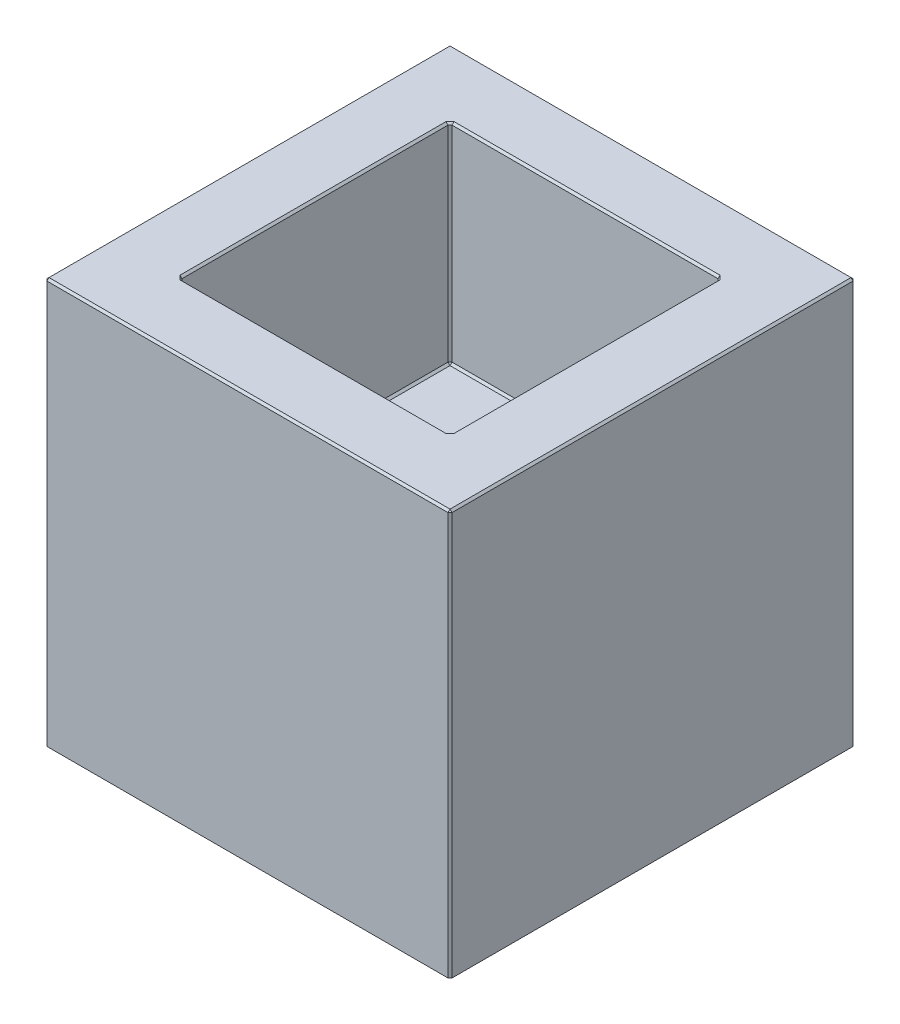
SolidWorks part; units mm, degrees
ref_plane "Plan de face" through (0, 0, 0) normal (0, 0, 1) x (1, 0, 0)
ref_plane "Plan de dessus" through (0, 0, 0) normal (0, 1, 0) x (1, 0, 0)
ref_plane "Plan de droite" through (0, 0, 0) normal (1, 0, 0) x (0, 0, -1)
sketch "Esquisse2" plane through (0, 0, 0) normal (0, 1, 0) x (1, 0, 0)
  line L1 (-3, -3) -> (3, -3)
  line L2 (-3, -3) -> (-3, 3)
  line L3 (-3, 3) -> (3, 3)
  line L4 (3, -3) -> (3, 3)
  line L5 (-3, -3) -> (3, 3) construction
  line L6 (-3, 3) -> (3, -3) construction
  point P0 (0, 0)
  dimension "D1" = 6
extrude "Boss.-Extru.1" add sketch "Esquisse2" along normal blind 6
sketch "Esquisse4" plane through (0, 6, 0) normal (0, 1, 0) x (1, 0, 0)
  line L1 (-2, -2) -> (2, -2)
  line L2 (-2, -2) -> (-2, 2)
  line L3 (-2, 2) -> (2, 2)
  line L4 (2, -2) -> (2, 2)
  line L5 (-2, -2) -> (2, 2) construction
  line L6 (-2, 2) -> (2, -2) construction
  point P0 (0, 0)
  dimension "D1" = 4
extrude "Enlèv. mat.-Extru.1" cut sketch "Esquisse4" against normal blind 3.1
chamfer "Chanfrein1" distance 0.03 angle 45 20 edges at (3, 3, -3) (-3, 3, -3) (-3, 3, 3) (3, 3, 3) (0, 6, 3) (-3, 6, 0) (0, 6, -3) (3, 6, 0) (2, 4.45, 2) (-2, 4.45, 2) (-2, 4.45, -2) (0, 2.9, 2) (-2, 2.9, 0) (0, 2.9, -2) (2, 2.9, 0) (2, 4.45, -2) (0, 6, 2) (-2, 6, 0) (0, 6, -2) (2, 6, 0)
